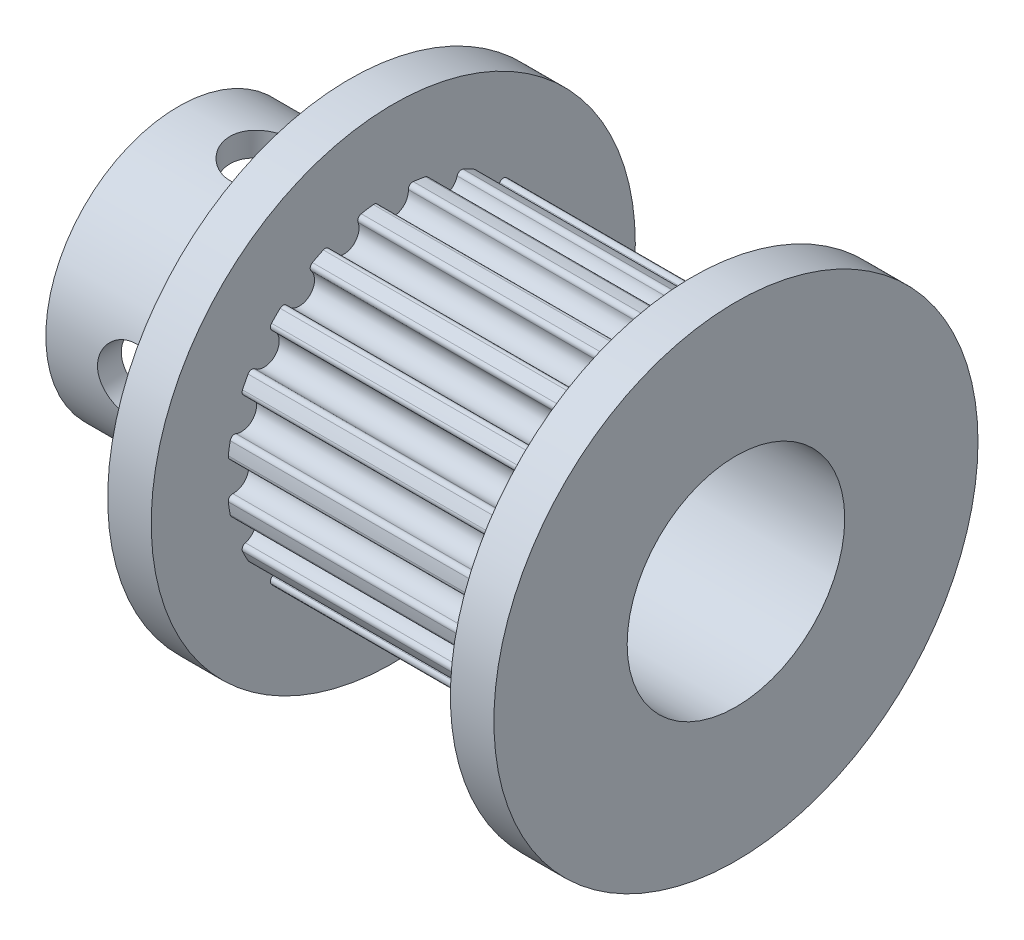
SolidWorks part; units mm, degrees
material "6061-T6 (SS)"
ref_plane "Front Plane" through (0, 0, 0) normal (0, 0, 1) x (1, 0, 0)
ref_plane "Top Plane" through (0, 0, 0) normal (0, 1, 0) x (1, 0, 0)
ref_plane "Right Plane" through (0, 0, 0) normal (1, 0, 0) x (0, 0, -1)
sketch "Sketch1" plane through (0, 0, 0) normal (0, 0, 1) x (1, 0, 0)
  line L0 (0, 4) -> (0, 4.875)
  line L1 (6.3, 8.9) -> (7.9, 8.9)
  line L2 (7.9, 8.9) -> (7.9, 6.11)
  line L3 (7.9, 6.11) -> (18.9, 6.11)
  line L4 (18.9, 6.11) -> (18.9, 8.9)
  line L5 (18.9, 8.9) -> (20.5, 8.9)
  line L6 (20.5, 8.9) -> (20.5, 4)
  line L7 (20.5, 4) -> (0, 4)
  line L8 (0, 0) -> (-7.6744, 0) construction
  line L9 (6.3, 8.9) -> (6.3, 4.875)
  line L10 (6.3, 4.875) -> (0, 4.875)
  dimension "D1" = 8
  dimension "D2" = 17.8
  dimension "D3" = 12.22
  dimension "D4" = 14.2
  dimension "D5" = 20.5
  dimension "D6" = 1.6
  dimension "D7" = 9.75
revolve "Revolve1" add sketch "Sketch1" angle 360 about L8
sketch "Croquis5" plane through (18.9, 0, 0) normal (-1, 0, 0) x (0, 0, 1)
  line L0 (0, 0) -> (0, 5.87) construction
  circle A0 centre (0, 5.87) radius 0.555
  circle A1 centre (1.8139, 5.5827) radius 0.555
  circle A2 centre (3.4503, 4.7489) radius 0.555
  circle A3 centre (4.7489, 3.4503) radius 0.555
  circle A4 centre (5.5827, 1.8139) radius 0.555
  circle A5 centre (5.87, 0) radius 0.555
  circle A6 centre (5.5827, -1.8139) radius 0.555
  circle A7 centre (4.7489, -3.4503) radius 0.555
  circle A8 centre (3.4503, -4.7489) radius 0.555
  circle A9 centre (1.8139, -5.5827) radius 0.555
  circle A10 centre (0, -5.87) radius 0.555
  circle A11 centre (-1.8139, -5.5827) radius 0.555
  circle A12 centre (-3.4503, -4.7489) radius 0.555
  circle A13 centre (-4.7489, -3.4503) radius 0.555
  circle A14 centre (-5.5827, -1.8139) radius 0.555
  circle A15 centre (-5.87, 0) radius 0.555
  circle A16 centre (-5.5827, 1.8139) radius 0.555
  circle A17 centre (-4.7489, 3.4503) radius 0.555
  circle A18 centre (-3.4503, 4.7489) radius 0.555
  circle A19 centre (-1.8139, 5.5827) radius 0.555
  dimension "D1" = 1.11
  dimension "D2" = 20
  dimension "D3" = 5.87
extrude "Cortar-Extruir1" cut sketch "Croquis5" along normal up to surface (11 mm away) up to face at (7.9, 0, -8.9)
fillet "Redondeo1" radius 0.16 40 edges at (13.4, 6.0887, -0.5101) (13.4, 6.0887, 0.5101) (13.4, 5.9483, 1.3964) (13.4, 5.633, 2.3666) (13.4, 5.2257, 3.1661) (13.4, 4.626, 3.9915) (13.4, 3.9915, 4.626) (13.4, 3.1661, 5.2257) (13.4, 2.3666, 5.633) (13.4, 1.3964, 5.9483) (13.4, 0.5101, 6.0887) (13.4, -0.5101, 6.0887) (13.4, -1.3964, 5.9483) (13.4, -2.3666, 5.633) (13.4, -3.1661, 5.2257) (13.4, -3.9915, 4.626) (13.4, -4.626, 3.9915) (13.4, -5.2257, 3.1661) (13.4, -5.633, 2.3666) (13.4, -5.9483, 1.3964) (13.4, -6.0887, 0.5101) (13.4, -6.0887, -0.5101) (13.4, -5.9483, -1.3964) (13.4, -5.633, -2.3666) (13.4, -5.2257, -3.1661) (13.4, -4.626, -3.9915) (13.4, -3.9915, -4.626) (13.4, -3.1661, -5.2257) (13.4, -2.3666, -5.633) (13.4, -1.3964, -5.9483) (13.4, -0.5101, -6.0887) (13.4, 0.5101, -6.0887) (13.4, 1.3964, -5.9483) (13.4, 2.3666, -5.633) (13.4, 3.1661, -5.2257) (13.4, 3.9915, -4.626) (13.4, 4.626, -3.9915) (13.4, 5.2257, -3.1661) (13.4, 5.633, -2.3666) (13.4, 5.9483, -1.3964)
hole_wizard "M3x0.5 Tapped Hole1" positions "Sketch3" profile "Sketch2" tap size "M3x0.5" standard "ANSI Metric"
sketch "Sketch3" plane through (0, 0, 0) normal (0, 1, 0) x (1, 0, 0)
  line L0 (0, 0) -> (6.3, 0) construction
  line L2 (6.3, 4.875) -> (6.3, -4.875) construction
  point P8 (3.15, 0)
sketch "Sketch2" plane through (3.15, 0, 0) normal (1, 0, 0) x (0, 0, -1)
  line L0 (0, 0) -> (0, 8.9)
  line L1 (0, 8.9) -> (1.25, 8.9)
  line L2 (1.25, 8.9) -> (1.25, 0)
  line L5 (1.25, 0) -> (0, 0)
  line L11 (0, -6.35) -> (0, 107.95) construction
  dimension "Thread Major Dia." = 2.5
  dimension "Thru Tap Drill Depth" = 8.9
hole_wizard "M3x0.5 Tapped Hole2" positions "Sketch5" profile "Sketch4" tap size "M3x0.5" standard "ANSI Metric"
sketch "Sketch5" plane through (0, 0, 0) normal (0, 0, 1) x (1, 0, 0)
  line L0 (0, 0) -> (6.3, 0) construction
  line L2 (6.3, 8.9) -> (6.3, -8.9) construction
  point P7 (3.15, 0)
sketch "Sketch4" plane through (3.15, 0, 0) normal (1, 0, 0) x (0, 1, 0)
  line L0 (0, 0) -> (0, 8.9)
  line L1 (0, 8.9) -> (1.25, 8.9)
  line L2 (1.25, 8.9) -> (1.25, 0)
  line L5 (1.25, 0) -> (0, 0)
  line L11 (0, -6.35) -> (0, 107.95) construction
  dimension "Thread Major Dia." = 2.5
  dimension "Thru Tap Drill Depth" = 8.9
sketch "Croquis1" plane through (0, 0, 0) normal (0, 1, 0) x (1, 0, 0)
  line L1 (-0.2603, 10.6382) -> (21.5762, 10.6382)
  line L2 (-0.2603, 10.6382) -> (-0.2603, -11.1983)
  line L3 (-0.2603, -11.1983) -> (21.5762, -11.1983)
  line L4 (21.5762, 10.6382) -> (21.5762, -11.1983)
sketch "Croquis2" plane through (0, 0, 0) normal (0, 0, 1) x (1, 0, 0)
  line L1 (-0.3065, 13.7163) -> (22.433, 13.7163)
  line L2 (-0.3065, 13.7163) -> (-0.3065, -14.2709)
  line L3 (-0.3065, -14.2709) -> (22.433, -14.2709)
  line L4 (22.433, 13.7163) -> (22.433, -14.2709)
ref_plane "Plano1" through (13.4, 0, 0) normal (1, 0, 0) x (0, 0, -1)
move or copy body "Sólido-Mover/Copiar1" [suppressed] bodies to move or copy 103
